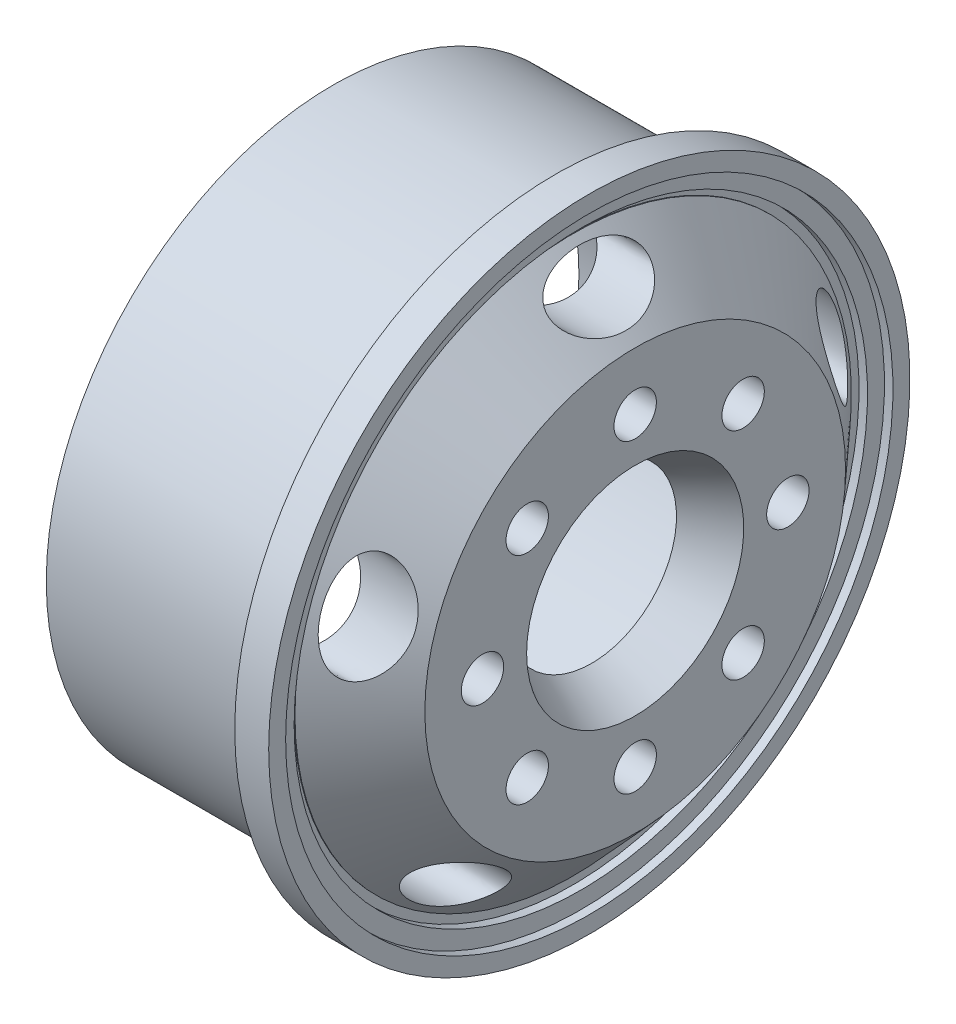
SolidWorks part; units mm, degrees
ref_plane "Front Plane" through (0, 0, 0) normal (0, 0, 1) x (1, 0, 0)
ref_plane "Top Plane" through (0, 0, 0) normal (0, 1, 0) x (1, 0, 0)
ref_plane "Right Plane" through (0, 0, 0) normal (1, 0, 0) x (0, 0, -1)
sketch "Sketch1" plane through (0, 0, 0) normal (0, 1, 0) x (1, 0, 0)
  line L0 (-37.2789, 0) -> (44.8184, 0) construction
  line L28 (4.7963, 16.9) -> (4.7963, 18.9)
  line L29 (4.7963, 18.9) -> (6.2963, 18.9)
  line L34 (6.9363, 11.4909) -> (6.9363, 5)
  line L37 (9.5014, 12.4) -> (9.5014, 6.4)
  line L39 (6.2963, 18.9) -> (6.7963, 18.9)
  line L40 (6.7963, 18.9) -> (6.7963, 17.9)
  line L41 (6.7963, 17.9) -> (6.2963, 17.9)
  line L45 (6.2963, 17.9) -> (6.2963, 16.9)
  line L46 (6.2963, 16.9) -> (5.7963, 16.9)
  line L50 (5.7963, 16.9) -> (5.7963, 16.4)
  line L53 (5.7963, 16.4) -> (5.8458, 16.4)
  line L54 (5.8458, 16.4) -> (9.5014, 12.4)
  line L55 (6.9363, 11.4909) -> (4.1863, 14.5)
  line L58 (6.9363, 5) -> (9.5014, 6.4)
  line L59 (4.7963, 16.9) -> (-8.3137, 16.9)
  line L60 (-8.3137, 16.9) -> (-8.3137, 14.5)
  line L61 (-8.3137, 14.5) -> (4.1863, 14.5)
  point P3 (8.936, 7.0891)
  point P4 (7.9363, 16.8502)
  point P5 (4.0798, 13.7427)
  point P16 (8.0798, 11.847)
  dimension "D2" = 10
  dimension "D4" = 12.5
  dimension "D5" = 1
  dimension "D6" = 1.5
  dimension "D8" = 137.576
  dimension "D9" = 2
  dimension "D10" = 1
  dimension "D11" = 0.5
  dimension "D3" = 13.11
  dimension "D13" = 0.5
  dimension "D17" = 37.8
  dimension "D18" = 4
  dimension "D19" = 22.9818
  dimension "D21" = 4.0764
  dimension "D22" = 2.75
  dimension "D23" = 3.0091
  dimension "D24" = 11.4909
  dimension "D25" = 6
  dimension "D14" = 0.5
revolve "Revolve1" add sketch "Sketch1" angle 360 about L0
sketch "Sketch2" plane through (9.5014, 0, 0) normal (1, 0, 0) x (0, 0, -1)
  circle A0 centre (0, 0) radius 9 construction
  circle A1 centre (0, 9) radius 1.25
  circle A2 centre (6.364, 6.364) radius 1.25
  circle A3 centre (9, 0) radius 1.25
  circle A4 centre (6.364, -6.364) radius 1.25
  circle A5 centre (0, -9) radius 1.25
  circle A6 centre (-6.364, -6.364) radius 1.25
  circle A7 centre (-9, 0) radius 1.25
  circle A8 centre (-6.364, 6.364) radius 1.25
  point P22 (0, 0)
  dimension "D1" = 18
  dimension "D2" = 2.5
  dimension "D3" = 8
extrude "Cut-Extrude1" cut sketch "Sketch2" against normal through all
ref_plane "Plane1" through (0, 0, 15) normal (0, 0, 1) x (1, 0, 0)
sketch "Sketch4" plane through (9.5014, 0, 0) normal (1, 0, 0) x (0, 0, -1)
  circle A0 centre (0, 0) radius 14.5 construction
  ellipse E0 centre (0, 14.5) end of major axis (3, 14.5) minor radius 1.5
  ellipse E1 centre (13.7903, 4.4807) end of major axis (14.7174, 1.6276) minor radius 1.5
  ellipse E2 centre (8.5229, -11.7307) end of major axis (6.0958, -13.4941) minor radius 1.5
  ellipse E3 centre (-8.5229, -11.7307) end of major axis (-10.9499, -9.9674) minor radius 1.5
  ellipse E4 centre (-13.7903, 4.4807) end of major axis (-14.7174, 1.6276) minor radius 1.5
  point P36 (0, 0)
  dimension "D1" = 29
  dimension "D2" = 6
  dimension "D3" = 3
  dimension "D4" = 5
extrude "Cut-Extrude3" cut sketch "Sketch4" against normal up to surface (5.5957 mm away)
